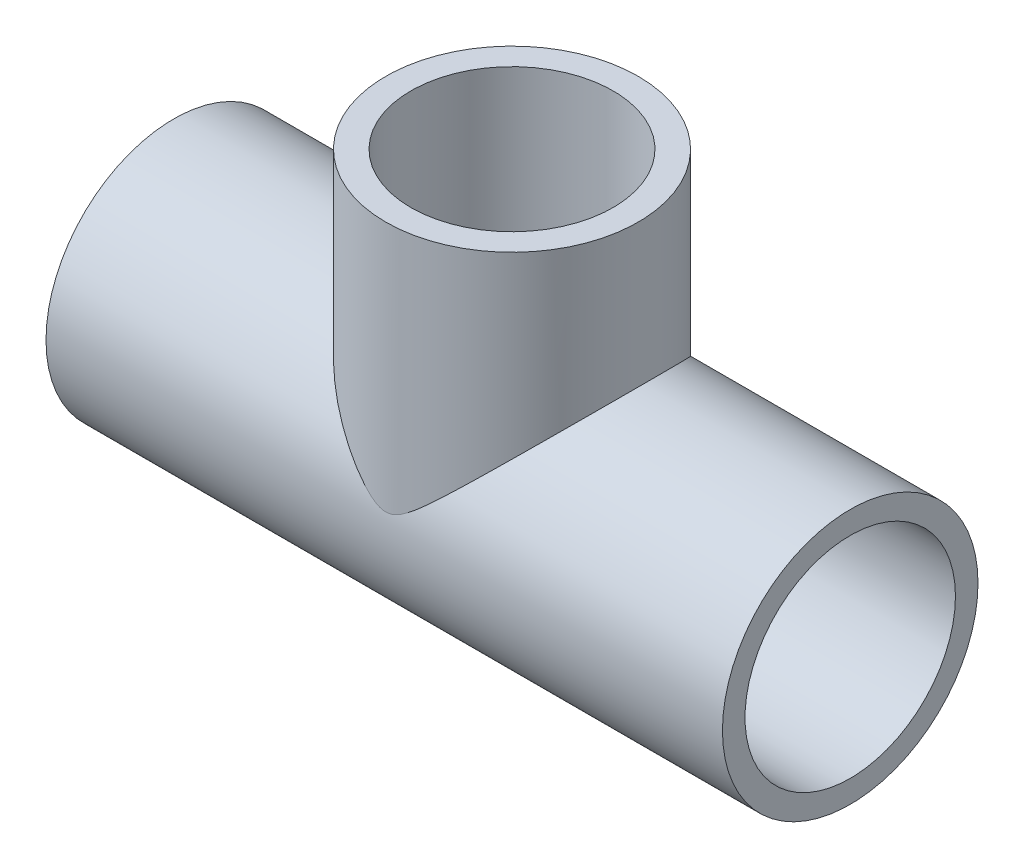
SolidWorks part; units mm, degrees
material "PVC 0.007 Plasticized"
ref_plane "Front Plane" through (0, 0, 0) normal (0, 0, 1) x (1, 0, 0)
ref_plane "Top Plane" through (0, 0, 0) normal (0, 1, 0) x (1, 0, 0)
ref_plane "Right Plane" through (0, 0, 0) normal (1, 0, 0) x (0, 0, -1)
sketch "Sketch2" plane through (0, 0, 0) normal (1, 0, 0) x (0, 0, -1)
  circle A0 centre (0, 0) radius 13.4938
  circle A1 centre (0, 0) radius 11.1125
  dimension "D1" = 26.9875
  dimension "D2" = 22.225
extrude "Boss-Extrude1" add sketch "Sketch2" against normal mid plane 71.4375
ref_plane "Plane1" through (0, 28.575, 0) normal (0, 1, 0) x (1, 0, 0)
sketch "Sketch4" plane through (0, 0, 0) normal (1, 0, 0) x (0, 0, -1)
  line L0 (0, 0) -> (0, 35.2701) construction
sketch "Sketch5" plane through (0, 28.575, 0) normal (0, 1, 0) x (1, 0, 0)
  circle A0 centre (0, 0) radius 13.335
  dimension "D1" = 26.67
extrude "Boss-Extrude2" add sketch "Sketch5" against normal blind 30.32
sketch "Sketch6" plane through (0, 28.575, 0) normal (0, 1, 0) x (1, 0, 0)
  circle A0 centre (0, 0) radius 10.6807
  dimension "D1" = 21.3614
extrude "Cut-Extrude1" cut sketch "Sketch6" against normal up to next
